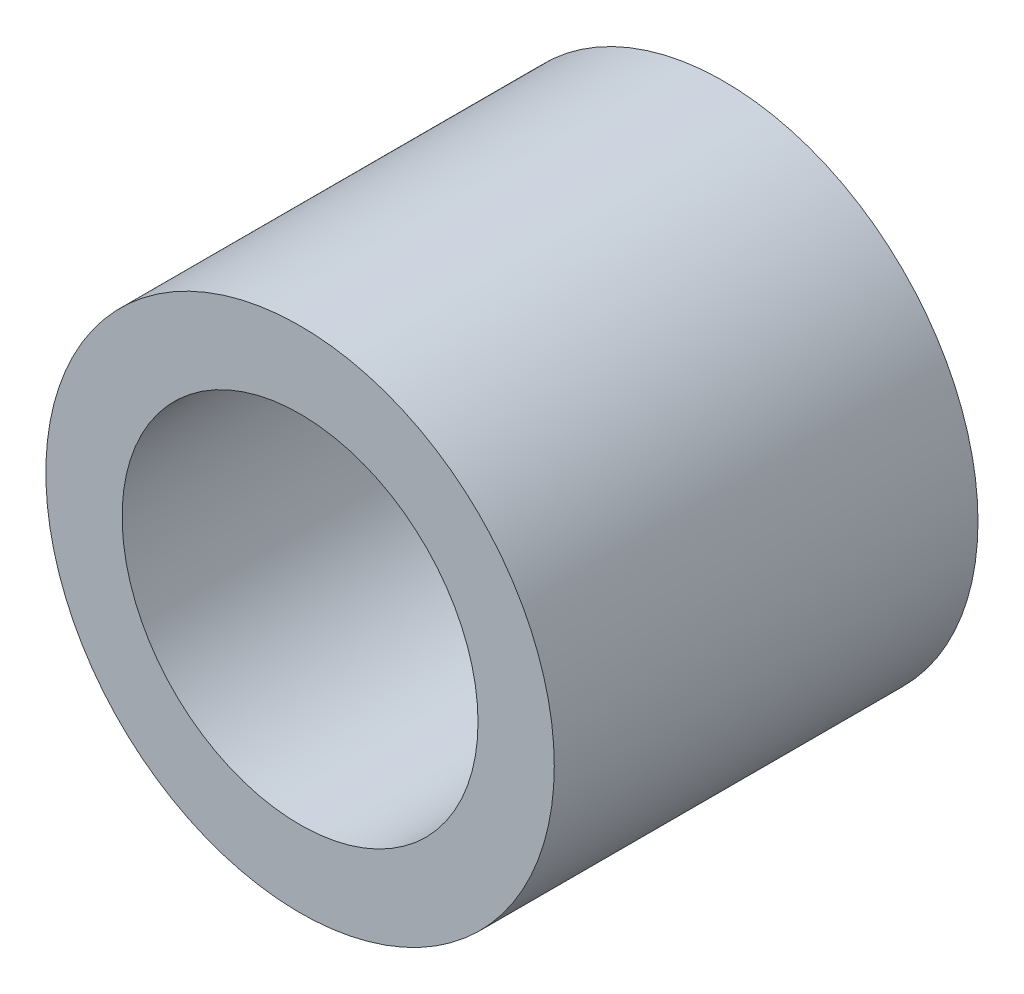
SolidWorks part; units mm, degrees
ref_plane "正面" through (0, 0, 0) normal (0, 0, 1) x (1, 0, 0)
ref_plane "平面" through (0, 0, 0) normal (0, 1, 0) x (1, 0, 0)
ref_plane "右側面" through (0, 0, 0) normal (1, 0, 0) x (0, 0, -1)
sketch "ｽｹｯﾁ1" plane through (0, 0, 0) normal (0, 0, 1) x (1, 0, 0)
  circle A0 centre (0, 0) radius 3
  circle A1 centre (0, 0) radius 2.1
  dimension "D1" = 4.2
  dimension "D2" = 6
extrude "ﾎﾞｽ - 押し出し1" add sketch "ｽｹｯﾁ1" along normal blind 5
